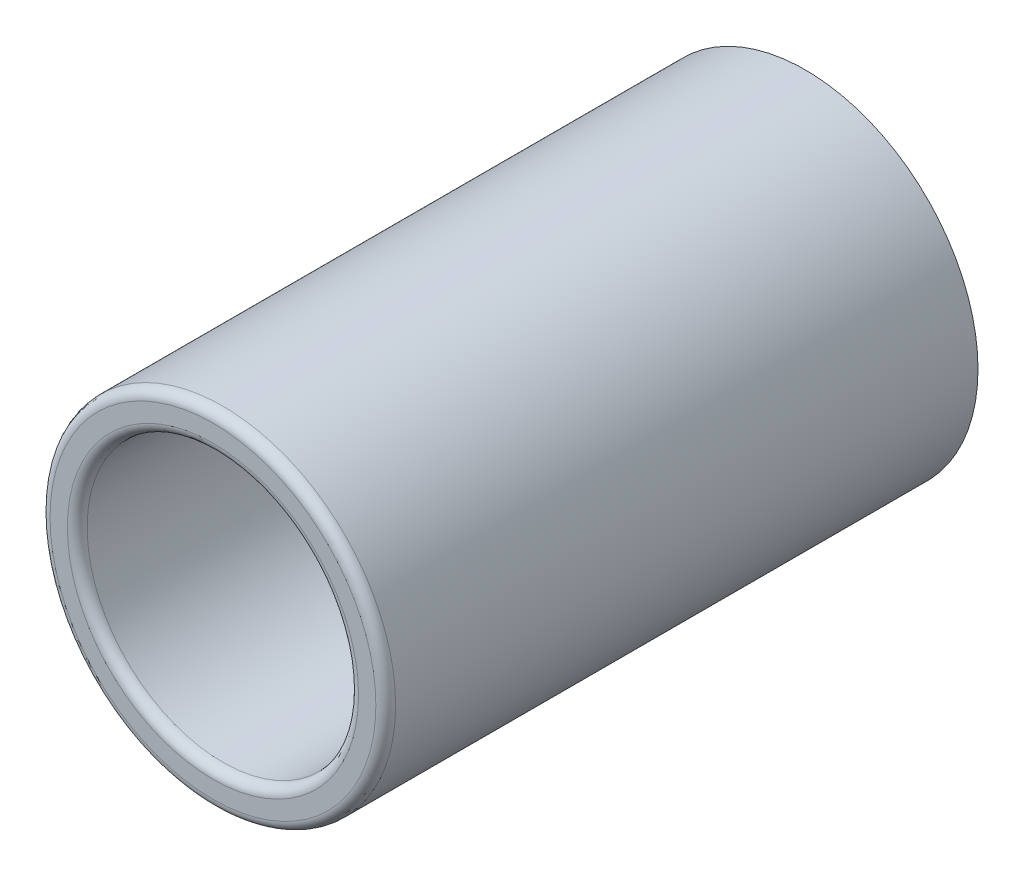
SolidWorks part; units mm, degrees
ref_plane "Front Plane" through (0, 0, 0) normal (0, 0, 1) x (1, 0, 0)
ref_plane "Top Plane" through (0, 0, 0) normal (0, 1, 0) x (1, 0, 0)
ref_plane "Right Plane" through (0, 0, 0) normal (1, 0, 0) x (0, 0, -1)
sketch "Sketch1" plane through (0, 0, 0) normal (0, 0, 1) x (1, 0, 0)
  circle A0 centre (0, 0) radius 2.75
  circle A1 centre (0, 0) radius 3.5
  dimension "D1" = 5.5
  dimension "D2" = 0.75
extrude "Boss-Extrude1" add sketch "Sketch1" along normal blind 12
fillet "Fillet1" radius 0.2 2 edges at (2.75, 0, 12) (3.5, 0, 12)
